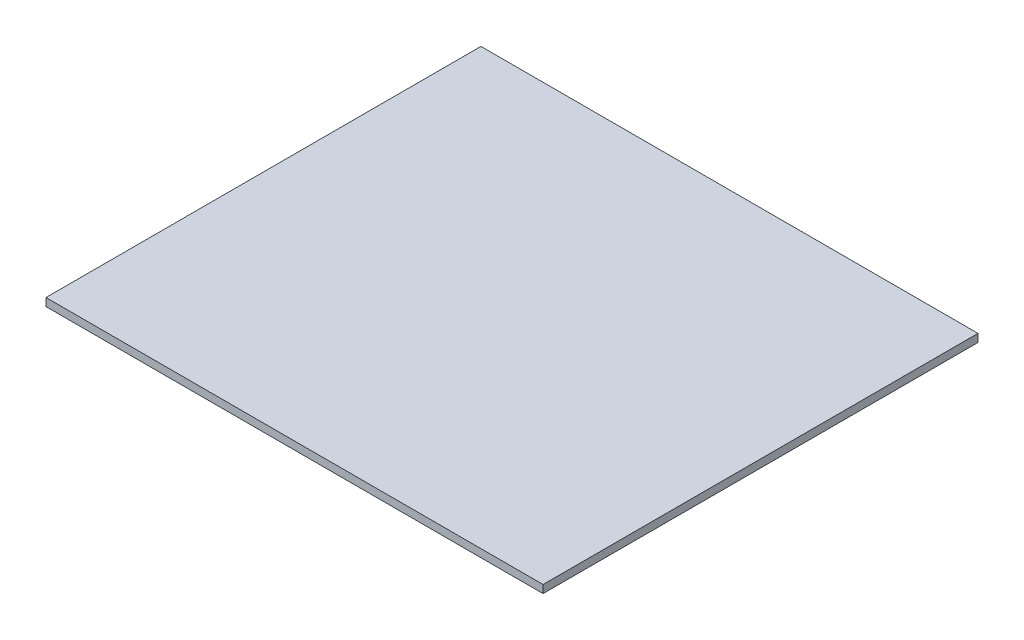
SolidWorks part; units mm, degrees
material "PC High Viscosity"
ref_plane "Front Plane" through (0, 0, 0) normal (0, 0, 1) x (1, 0, 0)
ref_plane "Top Plane" through (0, 0, 0) normal (0, 1, 0) x (1, 0, 0)
ref_plane "Right Plane" through (0, 0, 0) normal (1, 0, 0) x (0, 0, -1)
sketch "Sketch1" plane through (0, 0, 0) normal (0, 1, 0) x (1, 0, 0)
  line L1 (0, 0) -> (400, 0)
  line L2 (0, 0) -> (0, 350)
  line L3 (0, 350) -> (400, 350)
  line L4 (400, 0) -> (400, 350)
  dimension "D1" = 400
  dimension "D2" = 350
extrude "Boss-Extrude1" add sketch "Sketch1" along normal blind 6.35
